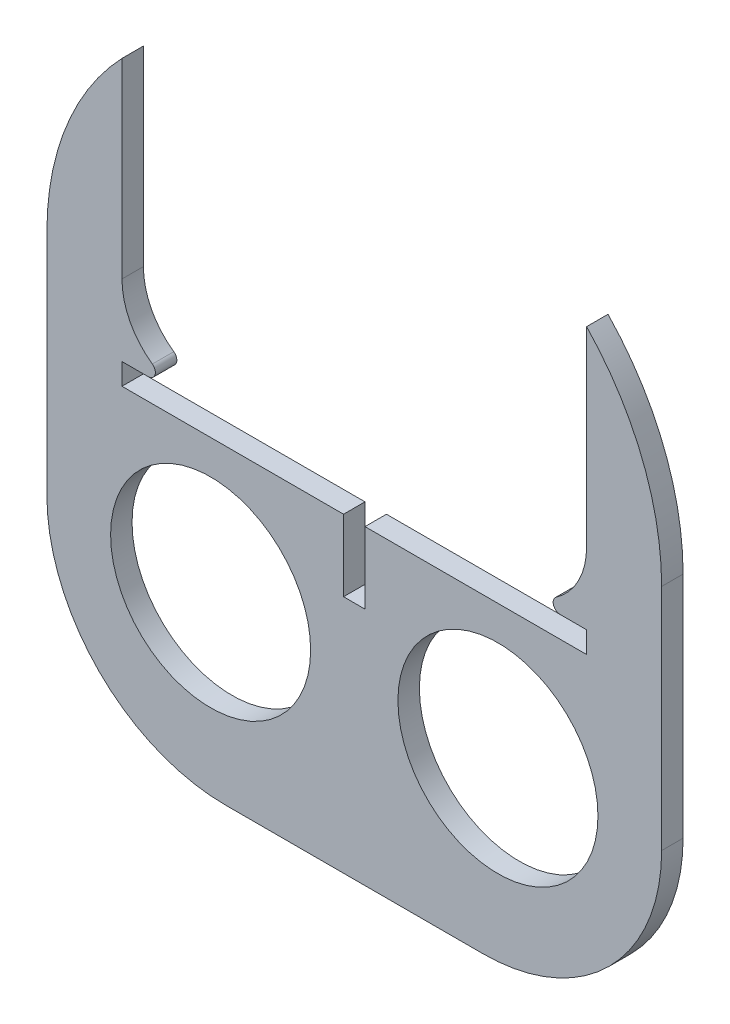
SolidWorks part; units mm, degrees
ref_plane "Front Plane" through (0, 0, 0) normal (0, 0, 1) x (1, 0, 0)
ref_plane "Top Plane" through (0, 0, 0) normal (0, 1, 0) x (1, 0, 0)
ref_plane "Right Plane" through (0, 0, 0) normal (1, 0, 0) x (0, 0, -1)
sketch "Sketch1" plane through (0, 0, 0) normal (0, 0, 1) x (1, 0, 0)
  line L0 (0, 8.5) -> (0, -86.5) construction
  line L1 (-43, 8.5) -> (43, 8.5) construction
  line L2 (-43, 8.5) -> (-43, -86.5) construction
  line L3 (-43, -86.5) -> (43, -86.5) construction
  line L4 (43, 8.5) -> (43, -86.5) construction
  line L5 (-5, 8.5) -> (5, 8.5)
  line L6 (-18, -86.5) -> (18, -86.5) construction
  line L7 (-43, -29.5) -> (43, -29.5) construction
  line L8 (-43, -29.5) -> (-43, -61.5)
  line L9 (-43, -61.5) -> (43, -61.5) construction
  line L10 (43, -29.5) -> (43, -61.5)
  line L11 (-0.5, -86.5) -> (0.5, -86.5) construction
  line L12 (-18, -86.5) -> (-0.5, -86.5)
  line L13 (0.5, -86.5) -> (18, -86.5)
  line L14 (-0.5, -86.5) -> (0.5, -86.5)
  line L15 (55, 0) -> (-55, 0) construction
  arc A0 (-43, -29.5) -> (-5, 8.5) centre (-5, -29.5) cw
  arc A1 (5, 8.5) -> (43, -29.5) centre (5, -29.5) cw
  arc A2 (-43, -61.5) -> (-18, -86.5) centre (-18, -61.5) ccw
  arc A3 (18, -86.5) -> (43, -61.5) centre (18, -61.5) ccw
  point P10 (0, 8.5)
  point P19 (0, -86.5)
  point P23 (0, -86.5)
  dimension "D3" = 25
  dimension "D4" = 38
  dimension "D1" = 95
  dimension "D2" = 86
  dimension "D5" = 1
  dimension "D6" = 8.5
extrude "Boss-Extrude1" add sketch "Sketch1" along normal blind 3
sketch "Sketch2" plane through (0, 0, 3) normal (0, 0, 1) x (1, 0, 0)
  line L0 (0, -1.65) -> (0, 1.65) construction
  line L1 (-22.5, -40) -> (22.5, -40)
  line L2 (-32.5, -30) -> (-32.5, 20)
  line L3 (-22.5, 30) -> (22.5, 30)
  line L4 (32.5, -30) -> (32.5, 20)
  line L5 (-32.5, -40) -> (32.5, 30) construction
  line L6 (-32.5, 30) -> (32.5, -40) construction
  line L7 (1.65, 0) -> (-1.65, 0) construction
  arc A0 (22.5, 30) -> (32.5, 20) centre (22.5, 20) cw
  arc A1 (22.5, -40) -> (32.5, -30) centre (22.5, -30) ccw
  arc A2 (-22.5, -40) -> (-32.5, -30) centre (-22.5, -30) cw
  arc A3 (-32.5, 20) -> (-22.5, 30) centre (-22.5, 20) cw
  point P0 (0, -5)
  dimension "D4" = 10
  dimension "D1" = 65
  dimension "D2" = 70
  dimension "D3" = 40
extrude "Cut-Extrude1" cut sketch "Sketch2" against normal blind 10
sketch "Sketch3" plane through (0, 0, 3) normal (0, 0, 1) x (1, 0, 0)
  line L0 (0, -1.65) -> (0, 1.65) construction
  line L1 (-32.5, -43) -> (32.5, -43)
  line L2 (-32.5, -43) -> (-32.5, -40)
  line L3 (-32.5, -40) -> (32.5, -40)
  line L4 (32.5, -43) -> (32.5, -40)
  line L5 (-32.5, -43) -> (32.5, -40) construction
  line L6 (-32.5, -40) -> (32.5, -43) construction
  line L7 (-22.5, -40) -> (22.5, -40) construction
  line L9 (-1.5, -53) -> (1.5, -53)
  line L10 (-1.5, -53) -> (-1.5, -43)
  line L11 (-1.5, -43) -> (1.5, -43)
  line L12 (1.5, -53) -> (1.5, -43)
  line L13 (-1.5, -53) -> (1.5, -43) construction
  line L14 (-1.5, -43) -> (1.5, -53) construction
  point P0 (0, -41.5)
  point P9 (0, -48)
  line M9 (22.5, -40) -> (-22.5, -40)
  dimension "D1" = 65
  dimension "D2" = 3
  dimension "D3" = 3
  dimension "D4" = 10
extrude "Cut-Extrude2" cut sketch "Sketch3" against normal blind 10 contours L1 L4 L3 L2 M9 | L9 L12 L1 L10
sketch "Sketch4" plane through (0, 0, 3) normal (0, 0, 1) x (1, 0, 0)
  line L0 (0, -1.65) -> (0, 1.65) construction
  circle A0 centre (-20.0977, -61.7663) radius 13.9919
  circle A1 centre (20.0977, -61.7663) radius 13.9919
extrude "Cut-Extrude3" cut sketch "Sketch4" against normal blind 10 contours A0 | A1
fillet "Fillet1" radius 1 2 edges at (22.5, -40, 1.5) (-22.5, -40, 1.5)
